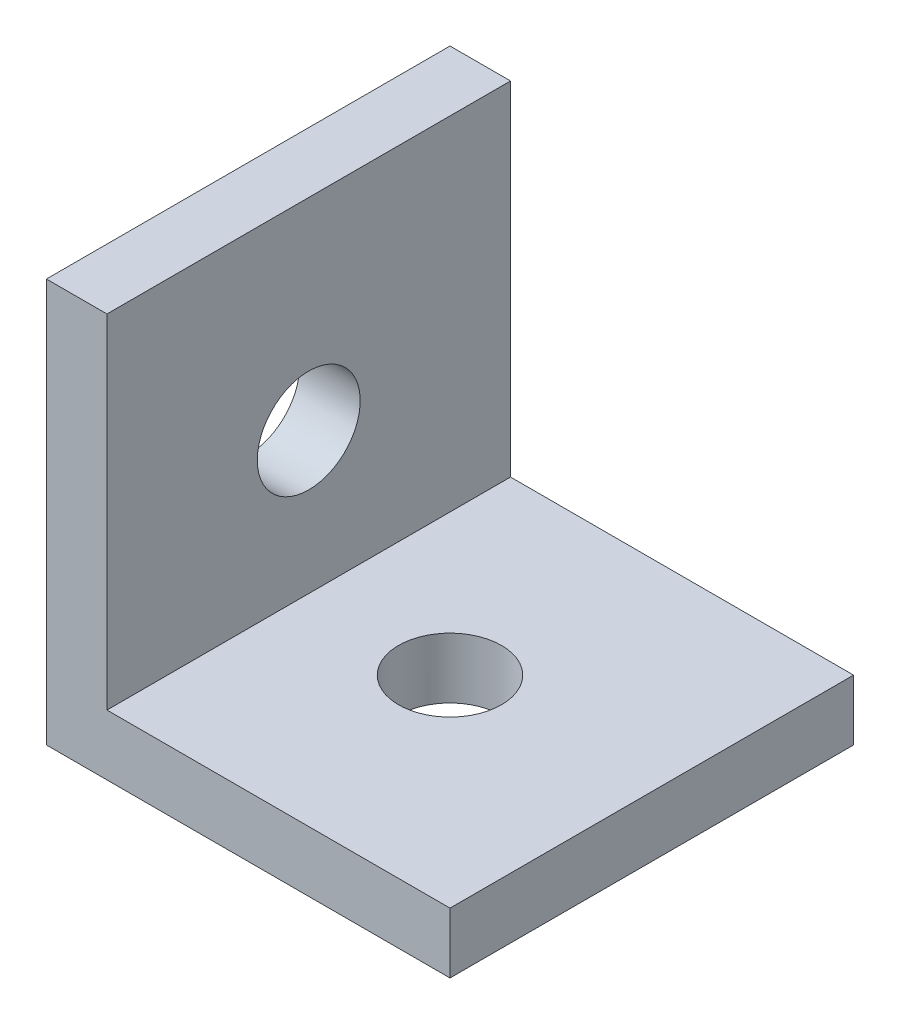
SolidWorks part; units mm, degrees
ref_plane "Front Plane" through (0, 0, 0) normal (0, 0, 1) x (1, 0, 0)
ref_plane "Top Plane" through (0, 0, 0) normal (0, 1, 0) x (1, 0, 0)
ref_plane "Right Plane" through (0, 0, 0) normal (1, 0, 0) x (0, 0, -1)
sketch "Sketch1" plane through (0, 0, 0) normal (0, 0, 1) x (1, 0, 0)
  line L0 (0, 20) -> (0, 0)
  line L1 (0, 0) -> (20, 0)
  line L2 (0, 20) -> (3, 20)
  line L3 (3, 20) -> (3, 3)
  line L4 (3, 3) -> (20, 3)
  line L5 (20, 3) -> (20, 0)
  dimension "D1" = 3
  dimension "D2" = 20
extrude "Boss-Extrude1" add sketch "Sketch1" along normal blind 20
sketch "Sketch2" plane through (0, 0, 0) normal (-1, 0, 0) x (0, 0, 1)
  line L0 (20, 20) -> (0, 20) construction
  line L1 (20, 20) -> (20, 0) construction
  line L2 (20, 0) -> (0, 0) construction
  circle A0 centre (10, 10) radius 2.55
  dimension "D1" = 10
  dimension "D2" = 10
  dimension "D3" = 5.1
extrude "Cut-Extrude1" cut sketch "Sketch2" against normal up to next
sketch "Sketch3" plane through (0, 0, 0) normal (0, -1, 0) x (1, 0, 0)
  line L0 (0, 20) -> (20, 20) construction
  line L2 (0, 20) -> (0, 0) construction
  circle A0 centre (10, 10) radius 2.55
  dimension "D1" = 10
  dimension "D2" = 10
  dimension "D3" = 5.1
extrude "Cut-Extrude2" cut sketch "Sketch3" against normal up to next
